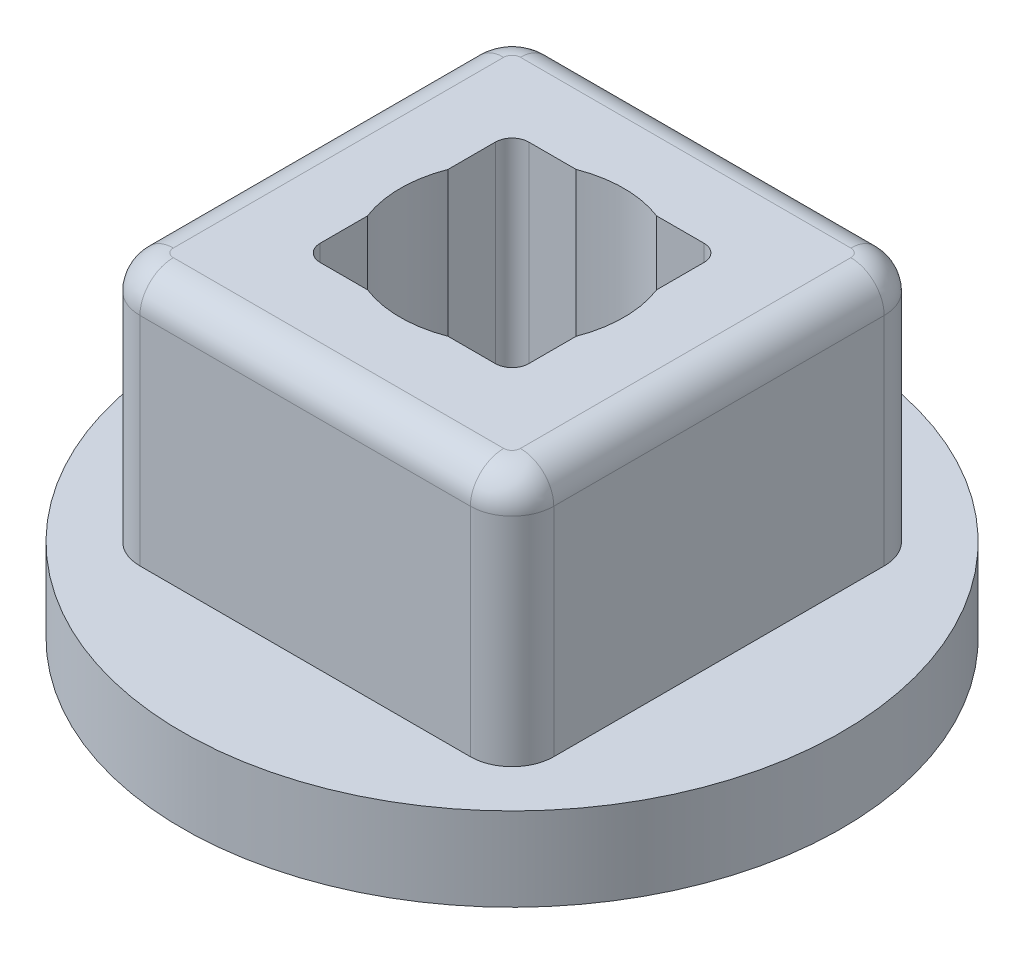
SolidWorks part; units mm, degrees
material "Custom Plastic"
ref_plane "Front Plane" through (0, 0, 0) normal (0, 0, 1) x (1, 0, 0)
ref_plane "Top Plane" through (0, 0, 0) normal (0, 1, 0) x (1, 0, 0)
ref_plane "Right Plane" through (0, 0, 0) normal (1, 0, 0) x (0, 0, -1)
sketch "Sketch1" plane through (0, 0, 0) normal (0, 0, 1) x (1, 0, 0)
  line L0 (5.0165, 1.27) -> (0, 1.27)
  line L1 (0, 1.27) -> (0, 0)
  line L2 (0, 0) -> (5.0165, 0)
  line L3 (5.0165, 0) -> (5.0165, 1.27)
  line L4 (0, 1.27) -> (0, 0) construction
revolve "Revolve1" add sketch "Sketch1" angle 360 about L4
sketch "Sketch2" plane through (0, 1.27, 0) normal (0, 1, 0) x (-1, 0, 0)
  line L0 (-3.1496, 3.1496) -> (3.1496, 3.1496)
  line L1 (3.1496, 3.1496) -> (3.1496, -3.1496)
  line L2 (3.1496, -3.1496) -> (-3.1496, -3.1496)
  line L3 (-3.1496, -3.1496) -> (-3.1496, 3.1496)
extrude "Boss-Extrude1" add sketch "Sketch2" along normal blind 3.81
sketch "Sketch3" plane through (0, 0, 0) normal (0, -1, 0) x (1, 0, 0)
  line L0 (-1.5875, -1.5875) -> (1.5875, -1.5875)
  line L1 (1.5875, -1.5875) -> (1.5875, 1.5875)
  line L2 (1.5875, 1.5875) -> (-1.5875, 1.5875)
  line L3 (-1.5875, 1.5875) -> (-1.5875, -1.5875)
extrude "Cut-Extrude1" cut sketch "Sketch3" against normal through all
fillet "Fillet1" radius 0.635 4 edges at (-3.1496, 3.175, 3.1496) (3.1496, 3.175, 3.1496) (-3.1496, 3.175, -3.1496) (3.1496, 3.175, -3.1496)
fillet "Fillet2" radius 0.254 4 edges at (-1.5875, 2.54, 1.5875) (-1.5875, 2.54, -1.5875) (1.5875, 2.54, -1.5875) (1.5875, 2.54, 1.5875)
fillet "Fillet3" radius 0.508 8 edges at (-3.1496, 5.08, 0) (-2.9636, 5.08, 2.9636) (-2.9636, 5.08, -2.9636) (0, 5.08, 3.1496) (0, 5.08, -3.1496) (2.9636, 5.08, 2.9636) (2.9636, 5.08, -2.9636) (3.1496, 5.08, 0)
sketch "Sketch4" plane through (0, 5.08, 0) normal (0, 1, 0) x (1, 0, 0)
  circle A0 centre (0, 0) radius 1.7018
extrude "Cut-Extrude2" cut sketch "Sketch4" against normal blind 51.054
